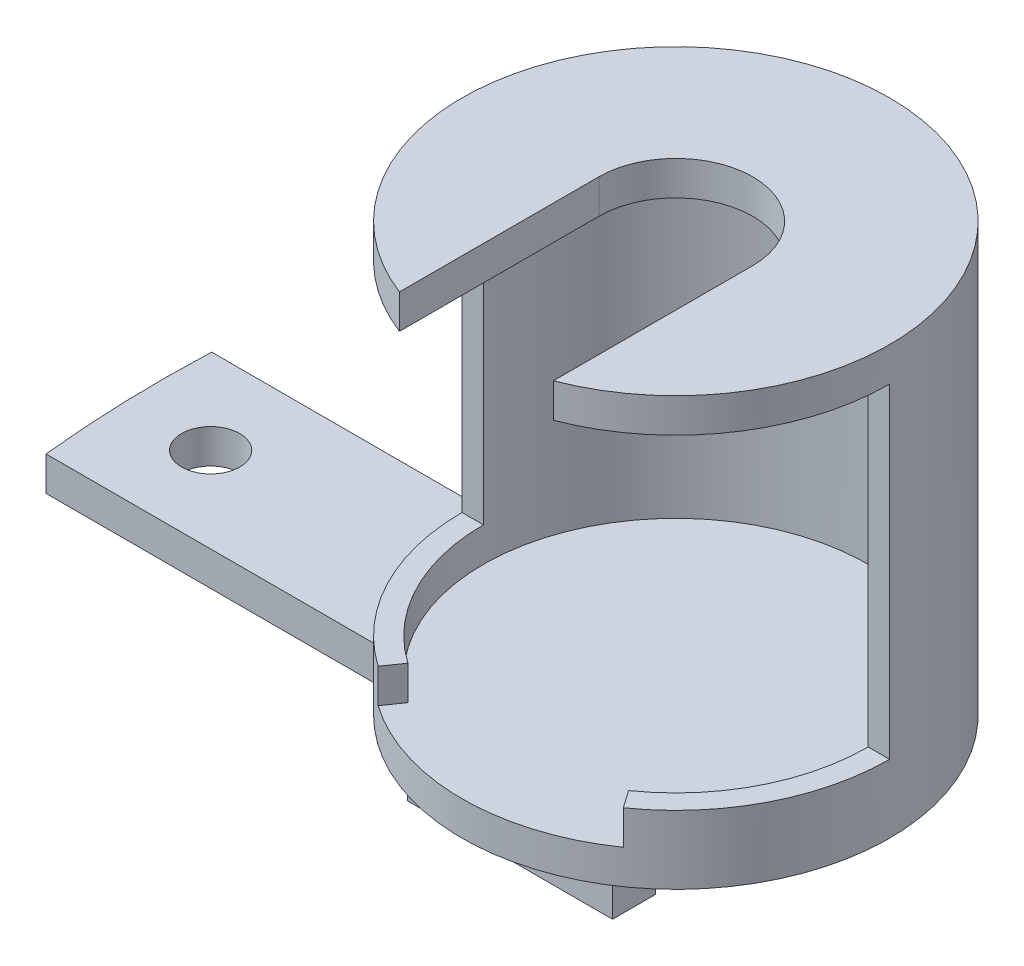
SolidWorks part; units mm, degrees
ref_plane "Alzado" through (0, 0, 0) normal (0, 0, 1) x (1, 0, 0)
ref_plane "Planta" through (0, 0, 0) normal (0, 1, 0) x (1, 0, 0)
ref_plane "Vista lateral" through (0, 0, 0) normal (1, 0, 0) x (0, 0, -1)
sketch "Croquis1" plane through (0, 0, 0) normal (0, 1, 0) x (1, 0, 0)
  circle A0 centre (0, 0) radius 11.25
  circle A1 centre (0, 0) radius 12.5
  dimension "D1" = 22.5
  dimension "D2" = 25
extrude "Saliente-Extruir1" add sketch "Croquis1" along normal blind 21
sketch "Croquis2" plane through (0, 21, 0) normal (0, 1, 0) x (1, 0, 0)
  line L0 (-12.5, 0) -> (12.5, 0)
  circle A0 centre (0, 0) radius 12.5 construction
  arc A1 (-12.5, 0) -> (12.5, 0) centre (0, 0) ccw
extrude "Cortar-Extruir1" cut sketch "Croquis2" against normal blind 19
sketch "Croquis3" plane through (0, 0, 0) normal (0, -1, 0) x (1, 0, 0)
  circle A0 centre (0, 0) radius 12.5 construction
  circle A1 centre (0, 0) radius 12.5
extrude "Saliente-Extruir2" add sketch "Croquis3" along normal blind 2
sketch "Croquis4" plane through (0, 21, 0) normal (0, 1, 0) x (1, 0, 0)
  line L0 (-4.5, 0) -> (-4.5, -11.6619)
  line L1 (4.5, 0) -> (4.5, -11.6619)
  circle A0 centre (0, 0) radius 12.5 construction
  arc A1 (4.5, -11.6619) -> (-4.5, -11.6619) centre (0, 0) ccw
  arc A2 (4.5, 0) -> (-4.5, 0) centre (0, 0) ccw
  dimension "D1" = 9
extrude "Saliente-Extruir3" add sketch "Croquis4" along normal blind 2
sketch "Croquis5" plane through (0, 2, 0) normal (0, 1, 0) x (1, 0, 0)
  line L0 (0, 0) -> (-7.1697, -10.2394)
  line L1 (0, 0) -> (7.1697, -10.2394)
  arc A0 (-12.5, 0) -> (12.5, 0) centre (0, 0) ccw construction
  arc A1 (-7.1697, -10.2394) -> (7.1697, -10.2394) centre (0, 0) ccw
  point P3 (0, -12.5)
  dimension "D1" = 70
extrude "Cortar-Extruir2" cut sketch "Croquis5" against normal up to surface (2 mm away) up to face at (0, 0, 11.25)
sketch "Croquis6" plane through (0, 0, 0) normal (0, 1, 0) x (1, 0, 0)
  line L3 (-29.6287, -7.2) -> (-10.2181, -7.2)
  line L9 (-21.0632, 2.8) -> (-21.0632, -7.2) construction
  line L12 (-29.944, 2.8) -> (-12.1824, 2.8)
  circle A0 centre (40, 0) radius 75 construction
  arc A2 (-29.944, 2.8) -> (-29.6287, -7.2) centre (40, 0) ccw
  circle A3 centre (0, 0) radius 12.5 construction
  arc A4 (-12.1824, 2.8) -> (-10.2181, -7.2) centre (0, 0) ccw
  circle A5 centre (-25, -2.2) radius 1.7
  point P4 (-21.0632, -2.2)
  dimension "D1" = 150
  dimension "D4" = 140
  dimension "D5" = 2.8
  dimension "D6" = 3.4
  dimension "D2" = 10
  dimension "D3" = 40
  dimension "D7" = 65
extrude "Saliente-Extruir4" add sketch "Croquis6" against normal up to surface (2 mm away) up to face at (0, -2, -12.5)
sketch "Croquis8" plane through (0, -2, 0) normal (0, -1, 0) x (1, 0, 0)
  line L0 (-29.6287, 7.2) -> (-10.2181, 7.2) construction
  line L1 (-6, 9.7) -> (6, 9.7)
  line L2 (-6, 9.7) -> (-6, 7.2)
  line L3 (-6, 7.2) -> (6, 7.2)
  line L4 (6, 9.7) -> (6, 7.2)
  line L5 (-6, 9.7) -> (6, 7.2) construction
  line L6 (-6, 7.2) -> (6, 9.7) construction
  line L7 (-6, -2.8) -> (6, -2.8)
  line L8 (-6, -2.8) -> (-6, -5.3)
  line L9 (-6, -5.3) -> (6, -5.3)
  line L10 (6, -2.8) -> (6, -5.3)
  line L11 (-6, -2.8) -> (6, -5.3) construction
  line L12 (-6, -5.3) -> (6, -2.8) construction
  line L13 (-12.1824, -2.8) -> (-29.944, -2.8) construction
  point P0 (0, 8.45)
  point P5 (0, -4.05)
  point P10 (0, -3.7921)
  point P11 (0, 7.9811)
  point P12 (0, 0)
  point P18 (-5.887, 7.2)
  dimension "D1" = 2.5
  dimension "D2" = 2.5
  dimension "D3" = 12
extrude "Saliente-Extruir5" add sketch "Croquis8" along normal blind 2.5
